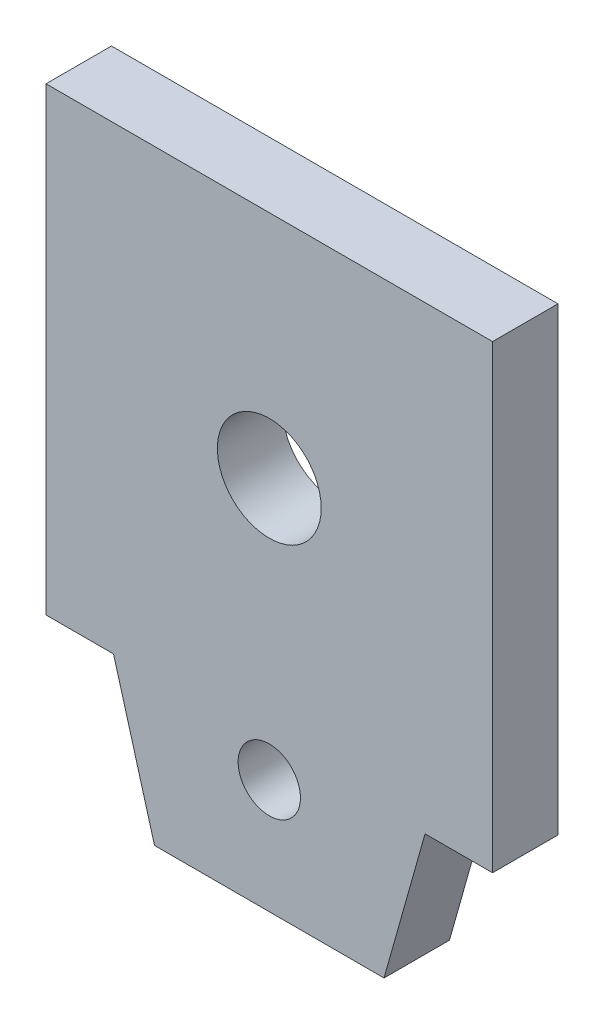
SolidWorks part; units mm, degrees
material "Fibre de verre A"
ref_plane "Plan de face" through (0, 0, 0) normal (0, 0, 1) x (1, 0, 0)
ref_plane "Plan de dessus" through (0, 0, 0) normal (0, 1, 0) x (1, 0, 0)
ref_plane "Plan de droite" through (0, 0, 0) normal (1, 0, 0) x (0, 0, -1)
sketch "Esquisse1" plane through (0, 0, 0) normal (0, 0, 1) x (1, 0, 0)
  line L0 (3.25, 0) -> (5.225, -7)
  line L1 (0, 0) -> (3.25, 0)
  line L2 (0, 0) -> (0, 22.15)
  line L3 (0, 22.15) -> (21.5, 22.15)
  line L4 (21.5, 0) -> (21.5, 22.15)
  line L5 (5.225, -7) -> (16.275, -7)
  line L6 (10.75, 22.15) -> (10.75, -6.9995) construction
  line L7 (18.25, 0) -> (21.5, 0)
  line L8 (18.25, 0) -> (16.275, -7)
  circle A0 centre (10.75, 11.075) radius 2.5
  circle A1 centre (10.75, -1.5) radius 1.5
  dimension "D9" = 3
  dimension "D10" = 5
  dimension "D1" = 21.5
  dimension "D2" = 22.15
  dimension "D3" = 3.25
  dimension "D4" = 11.05
  dimension "D5" = 7
  dimension "D6" = 3.25
  dimension "D7" = 1.975
  dimension "D8" = 1.5
  dimension "D11" = 11.075
extrude "Boss.-Extru.1" add sketch "Esquisse1" along normal blind 3.15
